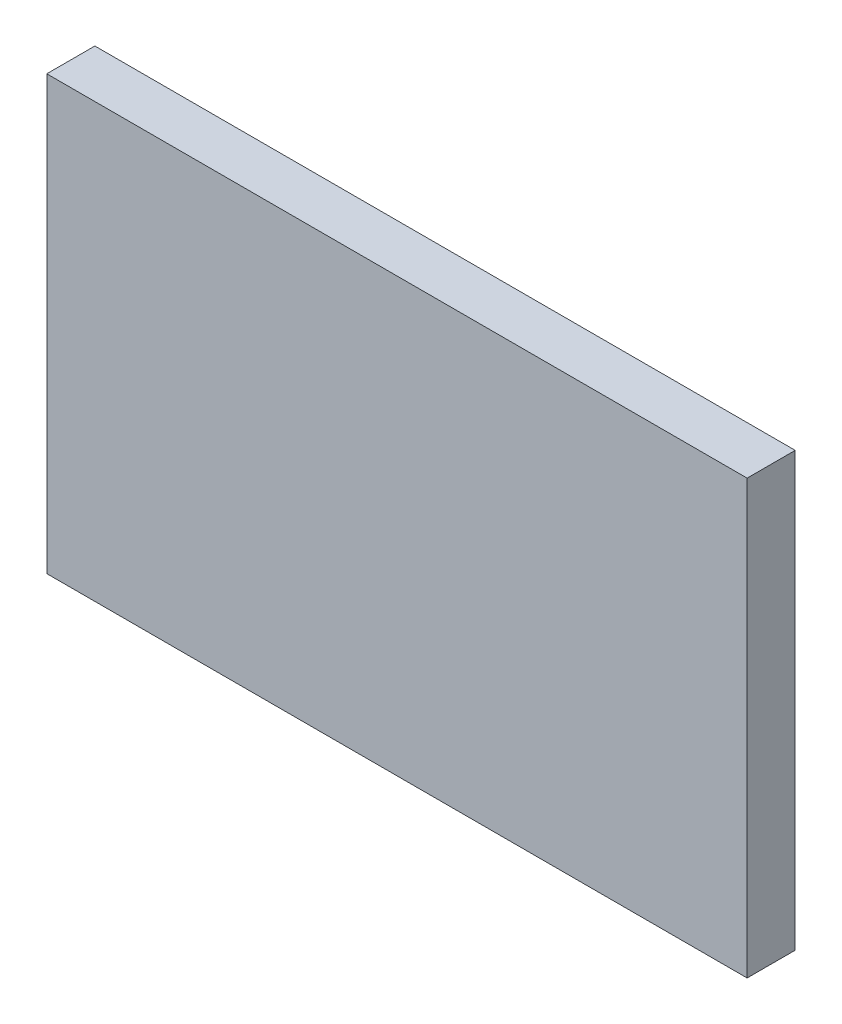
SolidWorks part; units mm, degrees
ref_plane "Front Plane" through (0, 0, 0) normal (0, 0, 1) x (1, 0, 0)
ref_plane "Top Plane" through (0, 0, 0) normal (0, 1, 0) x (1, 0, 0)
ref_plane "Right Plane" through (0, 0, 0) normal (1, 0, 0) x (0, 0, -1)
sketch "Sketch1" plane through (0, 0, 0) normal (0, 0, 1) x (1, 0, 0)
  line L1 (-23.114, -14.2875) -> (23.114, -14.2875)
  line L2 (-23.114, -14.2875) -> (-23.114, 14.2875)
  line L3 (-23.114, 14.2875) -> (23.114, 14.2875)
  line L4 (23.114, -14.2875) -> (23.114, 14.2875)
  line L5 (-23.114, -14.2875) -> (23.114, 14.2875) construction
  line L6 (-23.114, 14.2875) -> (23.114, -14.2875) construction
  point P0 (0, 0)
  dimension "D1" = 28.575
  dimension "D2" = 46.228
extrude "Boss-Extrude1" add sketch "Sketch1" along normal blind 3.175
